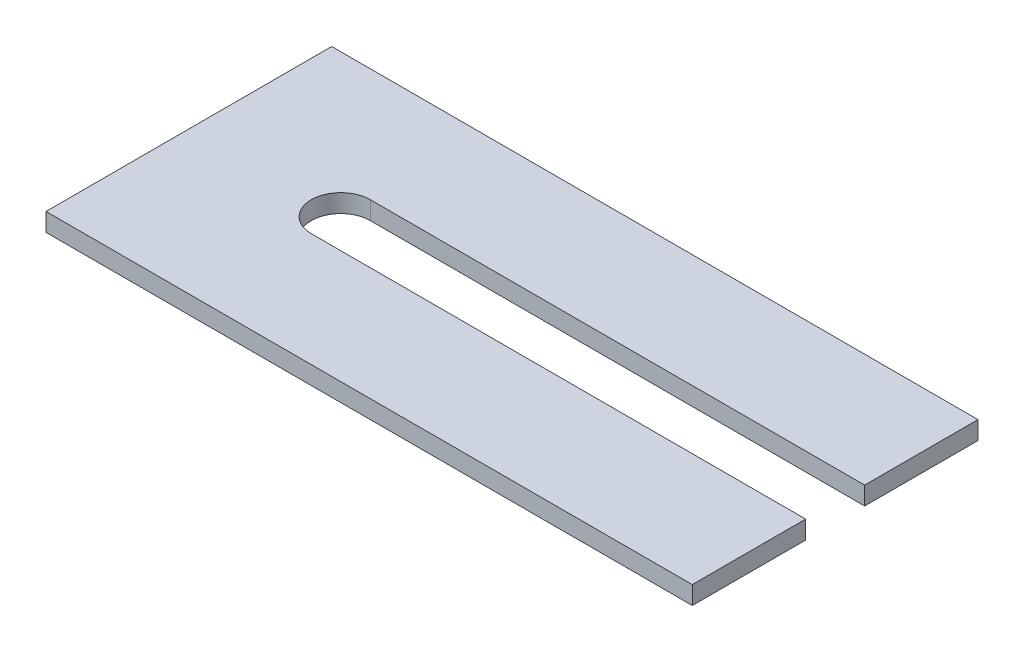
SolidWorks part; units mm, degrees
ref_plane "Front Plane" through (0, 0, 0) normal (0, 0, 1) x (1, 0, 0)
ref_plane "Top Plane" through (0, 0, 0) normal (0, 1, 0) x (1, 0, 0)
ref_plane "Right Plane" through (0, 0, 0) normal (1, 0, 0) x (0, 0, -1)
sketch "Sketch1" plane through (0, 0, 0) normal (0, 1, 0) x (1, 0, 0)
  line L0 (71.25, 15.75) -> (16.75, 15.75) construction
  line L1 (0, 0) -> (71.25, 0)
  line L2 (0, 0) -> (0, 31.5)
  line L3 (0, 31.5) -> (71.25, 31.5)
  line L4 (71.25, 0) -> (71.25, 31.5)
  line L5 (0, 0) -> (71.25, 31.5) construction
  line L6 (0, 31.5) -> (71.25, 0) construction
  line L7 (71.25, 12.5) -> (16.75, 12.5)
  line L8 (71.25, 19) -> (16.75, 19)
  line L9 (71.25, 19) -> (71.25, 12.5)
  arc A0 (71.25, 12.5) -> (71.25, 19) centre (71.25, 15.75) ccw
  arc A1 (16.75, 19) -> (16.75, 12.5) centre (16.75, 15.75) ccw
  point P4 (35.625, 15.75)
  point P8 (44, 15.75)
  point P13 (13.5, 15.75)
  dimension "D1" = 31.5
  dimension "D2" = 71.25
  dimension "D3" = 6.5
  dimension "D4" = 13.5
extrude "Boss-Extrude1" add sketch "Sketch1" along normal blind 2 contours A1 L8 L4 L3 L2 L1 L7
